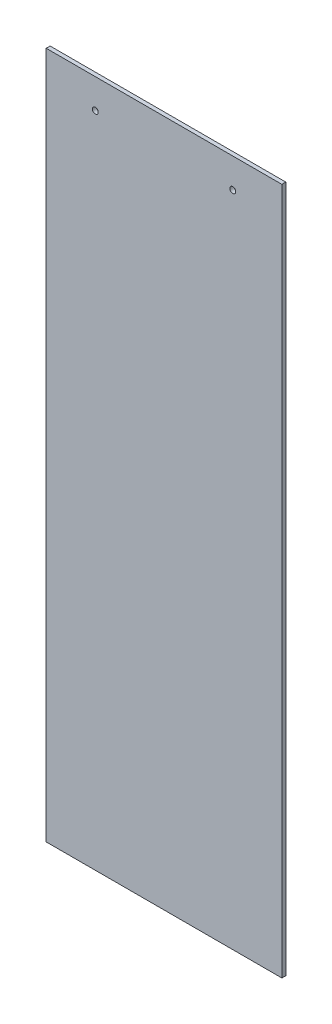
SolidWorks part; units mm, degrees
ref_plane "前视基准面" through (0, 0, 0) normal (0, 0, 1) x (1, 0, 0)
ref_plane "上视基准面" through (0, 0, 0) normal (0, 1, 0) x (1, 0, 0)
ref_plane "右视基准面" through (0, 0, 0) normal (1, 0, 0) x (0, 0, -1)
ref_plane "基准面4" through (0, 0, 2) normal (0, 0, 1) x (1, 0, 0)
sketch "草图1" plane through (0, 0, 2) normal (0, 0, 1) x (1, 0, 0)
  line L0 (-60, -175) -> (60, -175)
  line L1 (60, -175) -> (60, 175)
  line L2 (60, 175) -> (-60, 175)
  line L3 (-60, 175) -> (-60, -175)
  circle A0 centre (35, 160) radius 1.5
  circle A1 centre (-35, 160) radius 1.5
extrude "凸台-拉伸1" add sketch "草图1" against normal blind 2
